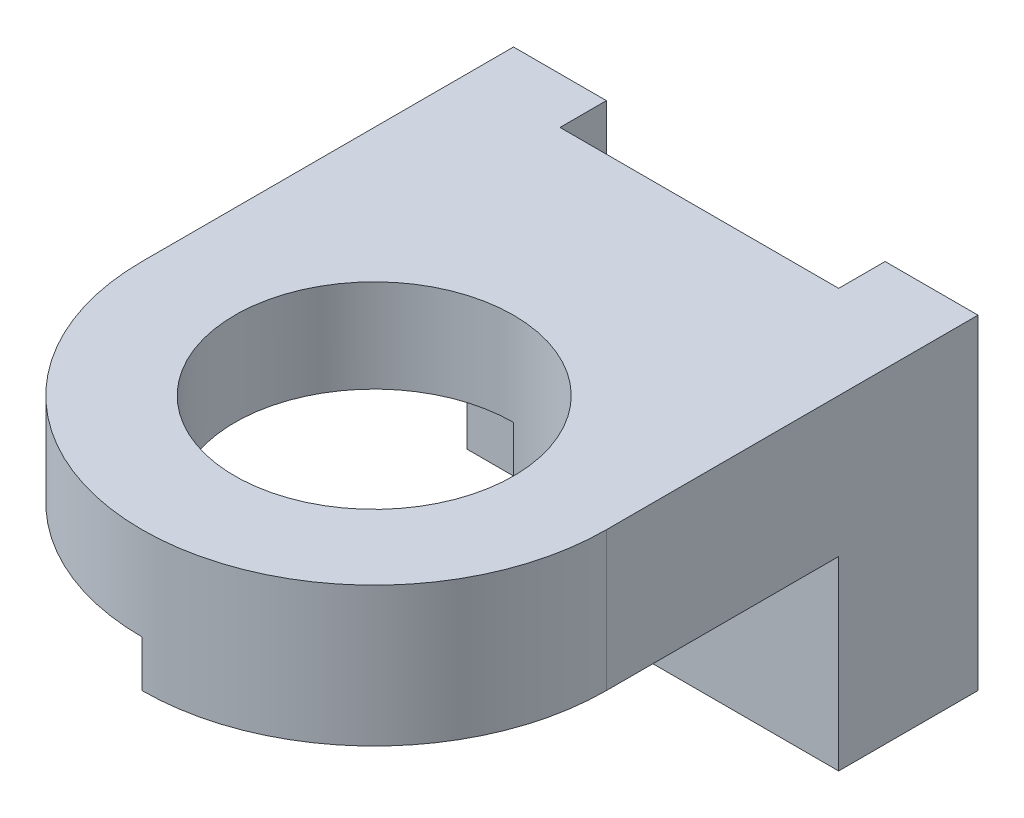
SolidWorks part; units mm, degrees
ref_plane "Front Plane" through (0, 0, 0) normal (0, 0, 1) x (1, 0, 0)
ref_plane "Top Plane" through (0, 0, 0) normal (0, 1, 0) x (1, 0, 0)
ref_plane "Right Plane" through (0, 0, 0) normal (1, 0, 0) x (0, 0, -1)
sketch "Sketch1" plane through (0, 0, 0) normal (0, 0, 1) x (1, 0, 0)
  line L1 (0, 0) -> (100, 0)
  line L2 (0, 0) -> (0, 40)
  line L3 (0, 40) -> (100, 40)
  line L4 (100, 0) -> (100, 40)
  dimension "D1" = 100
  dimension "D2" = 40
extrude "Boss-Extrude1" add sketch "Sketch1" along normal blind 30
sketch "Sketch2" plane through (0, 0, 30) normal (0, 0, 1) x (1, 0, 0)
  line L1 (0, 0) -> (50, 0)
  line L2 (0, 0) -> (0, 20)
  line L3 (0, 20) -> (50, 20)
  line L4 (50, 0) -> (50, 20)
  dimension "D1" = 50
  dimension "D2" = 20
extrude "Cut-Extrude1" cut sketch "Sketch2" against normal blind 30
sketch "Sketch3" plane through (0, 40, 0) normal (0, 1, 0) x (1, 0, 0)
  line L0 (100, 0) -> (0, 0) construction
  line L1 (80, 0) -> (20, 0)
  line L2 (80, 0) -> (80, -10)
  line L3 (80, -10) -> (20, -10)
  line L4 (20, 0) -> (20, -10)
  line L5 (100, -30) -> (100, 0) construction
  dimension "D1" = 10
  dimension "D2" = 20
  dimension "D3" = 20
extrude "Cut-Extrude3" cut sketch "Sketch3" against normal blind 110
sketch "Sketch4" plane through (0, 40, 0) normal (0, 1, 0) x (1, 0, 0)
  line L0 (100, 0) -> (100, -30)
  line L1 (100, -30) -> (0, -30)
  line L2 (0, -30) -> (0, 0)
  line L3 (0, 0) -> (20, 0)
  line L4 (100, 0) -> (80, 0)
  line L5 (80, 0) -> (80, -10)
  line L6 (80, -10) -> (20, -10)
  line L7 (20, -10) -> (20, 0)
extrude "Boss-Extrude2" add sketch "Sketch4" along normal blind 10
sketch "Sketch5" plane through (0, 0, 30) normal (0, 0, 1) x (1, 0, 0)
  line L0 (0, 50) -> (0, 20) construction
  line L1 (100, 50) -> (0, 50)
  line L2 (100, 50) -> (100, 40)
  line L3 (100, 40) -> (0, 40)
  line L4 (0, 50) -> (0, 40)
  dimension "D1" = 10
extrude "Boss-Extrude3" add sketch "Sketch5" along normal blind 10
sketch "Sketch6" plane through (0, 50, 0) normal (0, 1, 0) x (1, 0, 0)
  line L0 (0, -10) -> (30, -40)
  line L1 (0, 0) -> (0, -40) construction
  line L2 (100, -40) -> (0, -40) construction
  line L3 (30, -40) -> (0, -40)
  line L4 (0, -40) -> (0, -10)
  dimension "D1" = 10
  dimension "D2" = 30
extrude "Cut-Extrude4" cut sketch "Sketch6" against normal blind 45
sketch "Sketch7" plane through (0, 50, 0) normal (0, 1, 0) x (1, 0, 0)
  line L1 (0, 0) -> (100, 0)
  line L2 (0, 0) -> (0, -130)
  line L3 (0, -130) -> (100, -130)
  line L4 (100, 0) -> (100, -130)
  dimension "D1" = 100
  dimension "D2" = 130
extrude "Boss-Extrude4" add sketch "Sketch7" along normal blind 20
sketch "Sketch8" plane through (0, 50, 0) normal (0, -1, 0) x (1, 0, 0)
  circle A0 centre (50, 80) radius 30
  dimension "D1" = 60
  dimension "D3" = 50
  dimension "D2" = 40
extrude "Cut-Extrude5" cut sketch "Sketch8" against normal blind 20
sketch "Sketch9" plane through (0, 50, 0) normal (0, -1, 0) x (-1, 0, 0)
  line L0 (0, -10) -> (0, -130) construction
  line L1 (0, -80) -> (0, -130)
  line L2 (0, -130) -> (-100, -130)
  line L3 (-100, -130) -> (-100, -80)
  arc A0 (0, -80) -> (-100, -80) centre (-50, -80) cw
  point P14 (-49.4452, -130)
  line M4 (-100, -40) -> (-100, -130)
  line M5 (-100, -130) -> (0, -130)
  line M6 (0, -130) -> (0, -10)
  dimension "D1" = 50
  dimension "D2" = 50
  dimension "D3" = 100
  dimension "D4" = 50
  dimension "D5" = 50
extrude "Cut-Extrude6" cut sketch "Sketch9" against normal blind 20 contours A0 L2 M6 | A0 M5 M4
sketch "Sketch10" plane through (0, 50, 0) normal (0, -1, 0) x (-1, 0, 0)
  line L0 (-100, -80) -> (-100, -40) construction
  line L1 (-50, -110) -> (-50, -130)
  line L2 (-100, -80) -> (-100, -40)
  line L3 (-100, -40) -> (-50, -40)
  line L4 (-100, -40) -> (-30, -40) construction
  line L5 (-50, -40) -> (-50, -50)
  arc A0 (-50, -130) -> (-100, -80) centre (-50, -80) cw
  arc A1 (-100, -80) -> (0, -80) centre (-50, -80) ccw construction
  arc A2 (-50, -110) -> (-50, -50) centre (-50, -80) cw
  circle A3 centre (-50, -80) radius 30 construction
  dimension "D1" = 20
extrude "Boss-Extrude5" add sketch "Sketch10" along normal blind 10
sketch "Sketch12" plane through (0, 50, 0) normal (0, -1, 0) x (1, 0, 0)
  line L1 (20, 10) -> (80, 10)
  line L2 (20, 10) -> (20, 0)
  line L3 (20, 0) -> (80, 0)
  line L4 (80, 10) -> (80, 0)
extrude "Cut-Extrude9" cut sketch "Sketch12" against normal blind 56
